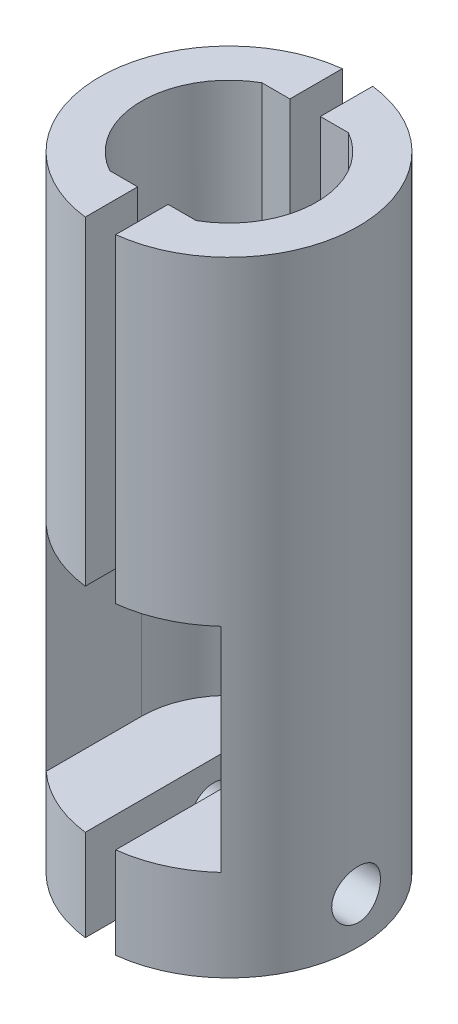
SolidWorks part; units mm, degrees
material "PET"
ref_plane "Спереди" through (0, 0, 0) normal (0, 0, 1) x (1, 0, 0)
ref_plane "Сверху" through (0, 0, 0) normal (0, 1, 0) x (1, 0, 0)
ref_plane "Справа" through (0, 0, 0) normal (1, 0, 0) x (0, 0, -1)
sketch "Эскиз1" plane through (0, 0, 0) normal (0, 1, 0) x (1, 0, 0)
  line L0 (0, 8.5) -> (0, -9.905) construction
  line L1 (2.8395, 5) -> (1, 5)
  line L3 (2.8395, -5) -> (1, -5)
  line L5 (2.8395, 5) -> (-2.8395, -5) construction
  line L6 (2.8395, -5) -> (-2.8395, 5) construction
  line L7 (1, 8.441) -> (1, 5)
  line L8 (-11.0455, 0) -> (16.2542, 0) construction
  line L9 (-1, 8.441) -> (-1, 5)
  line L10 (-1, -8.441) -> (-1, -5)
  line L11 (1, -8.441) -> (1, -5)
  line L12 (-1, -5) -> (-2.8395, -5)
  line L13 (-1, 5) -> (-2.8395, 5)
  arc A0 (1, -8.441) -> (1, 8.441) centre (0, 0) ccw
  arc A1 (-2.8395, 5) -> (-2.8395, -5) centre (0, 0) ccw
  arc A2 (2.8395, -5) -> (2.8395, 5) centre (0, 0) ccw
  arc A3 (-1, 8.441) -> (-1, -8.441) centre (0, 0) ccw
  dimension "D1" = 17
  dimension "D2" = 11.5
  dimension "D3" = 10
  dimension "D4" = 1
extrude "Бобышка-Вытянуть1" add sketch "Эскиз1" along normal blind 21
sketch "Эскиз3" plane through (0, 0, 0) normal (0, -1, 0) x (1, 0, 0)
  line L0 (1, -8.441) -> (1, -5) construction
  line L1 (1, -5) -> (2.8395, -5) construction
  line L2 (-2.8395, -5) -> (-1, -5) construction
  line L3 (-1, -5) -> (-1, -8.441) construction
  line L4 (1, -8.441) -> (1, -5)
  line L5 (1, -5) -> (2.8395, -5)
  line L6 (-2.8395, -5) -> (-1, -5)
  line L7 (-1, -5) -> (-1, -8.441)
  line L8 (5.75, 0) -> (5.75, 6.26)
  line L9 (-5.75, 0) -> (-5.75, 6.26)
  arc A0 (1, -8.441) -> (5.75, 6.26) centre (0, 0) ccw
  arc A1 (2.8395, -5) -> (2.8395, 5) centre (0, 0) ccw construction
  arc A2 (-2.8395, 5) -> (-2.8395, -5) centre (0, 0) ccw construction
  arc A3 (2.8395, -5) -> (5.75, 0) centre (0, 0) ccw
  arc A4 (-5.75, 0) -> (-2.8395, -5) centre (0, 0) ccw
  arc A5 (-5.75, 6.26) -> (-1, -8.441) centre (0, 0) ccw
extrude "Бобышка-Вытянуть2" add sketch "Эскиз3" along normal blind 14
sketch "Эскиз4" plane through (0, -14, 0) normal (0, -1, 0) x (1, 0, 0)
  line L0 (-1, 8.441) -> (-1, -8.441)
  line L1 (1, 8.441) -> (1, -8.441)
  arc A0 (1, -8.441) -> (1, 8.441) centre (0, 0) ccw
  arc A1 (-1, 8.441) -> (-1, -8.441) centre (0, 0) ccw
extrude "Бобышка-Вытянуть3" add sketch "Эскиз4" along normal blind 6
sketch "Эскиз6" plane through (0, 0, 0) normal (1, 0, 0) x (0, 0, -1)
  line L0 (-8.441, -20) -> (8.441, -20) construction
  circle A0 centre (0, -17) radius 1.6
  dimension "D1" = 3.2
  dimension "D2" = 3
extrude "Вырез-Вытянуть1" cut sketch "Эскиз6" against normal through all both and the other way through all
